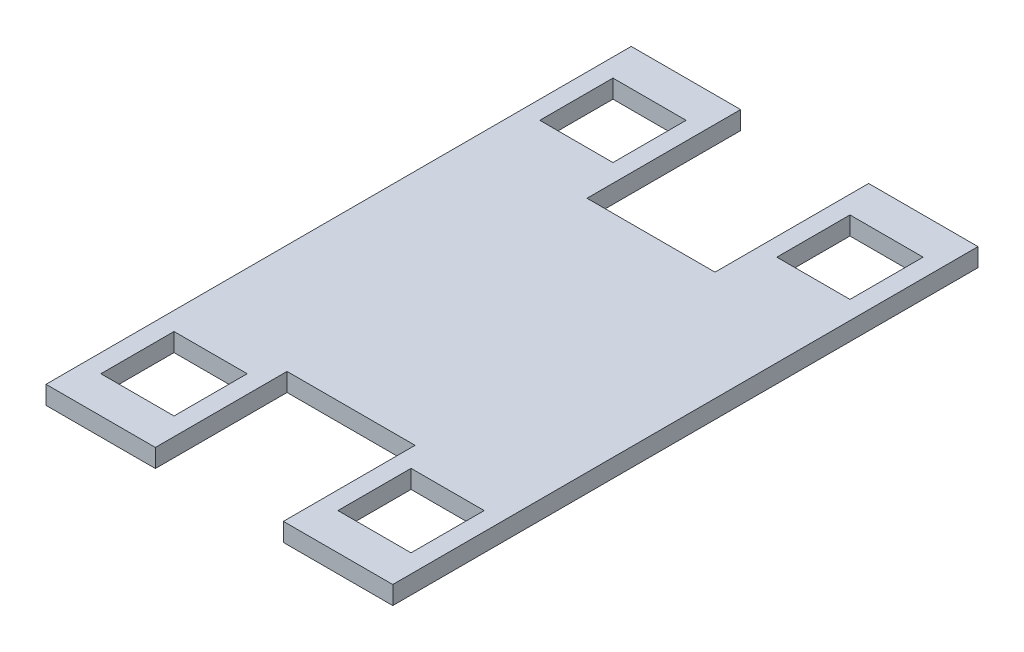
SolidWorks part; units mm, degrees
material "Balsa"
ref_plane "Front Plane" through (0, 0, 0) normal (0, 0, 1) x (1, 0, 0)
ref_plane "Top Plane" through (0, 0, 0) normal (0, 1, 0) x (1, 0, 0)
ref_plane "Right Plane" through (0, 0, 0) normal (1, 0, 0) x (0, 0, -1)
sketch "Sketch1" plane through (0, 0, 0) normal (0, 1, 0) x (1, 0, 0)
  line L1 (-60.198, 101.6) -> (60.198, 101.6)
  line L2 (-60.198, 101.6) -> (-60.198, -101.6)
  line L3 (-60.198, -101.6) -> (60.198, -101.6)
  line L4 (60.198, 101.6) -> (60.198, -101.6)
  line L5 (-60.198, 101.6) -> (60.198, -101.6) construction
  line L6 (-60.198, -101.6) -> (60.198, 101.6) construction
  point P0 (0, 0)
  dimension "D1" = 203.2
  dimension "D2" = 120.396
extrude "Boss-Extrude1" add sketch "Sketch1" along normal blind 6.35
sketch "Sketch2" plane through (0, 6.35, 0) normal (0, 1, 0) x (1, 0, 0)
  line L0 (-60.198, 101.6) -> (-60.198, -101.6) construction
  line L1 (-53.848, 88.9) -> (-28.448, 88.9)
  line L2 (-53.848, 88.9) -> (-53.848, 63.5)
  line L3 (-53.848, 63.5) -> (-28.448, 63.5)
  line L4 (-28.448, 88.9) -> (-28.448, 63.5)
  line L5 (-53.848, 88.9) -> (-28.448, 63.5) construction
  line L6 (-53.848, 63.5) -> (-28.448, 88.9) construction
  line L7 (60.198, 101.6) -> (-60.198, 101.6) construction
  point P0 (-41.148, 76.2)
  dimension "D1" = 6.35
  dimension "D2" = 12.7
  dimension "D3" = 25.4
extrude "Cut-Extrude1" cut sketch "Sketch2" against normal through all both and the other way through all
mirror "Mirror1" about plane through (0, 0, 0) normal (0, 0, 1) of "Cut-Extrude1"
mirror "Mirror2" about plane through (0, 0, 0) normal (1, 0, 0) of "Mirror1", "Cut-Extrude1"
sketch "Sketch3" plane through (0, 6.35, 0) normal (0, 1, 0) x (1, 0, 0)
  line L0 (0, -101.6) -> (0, 0) construction
  line L1 (-60.198, -101.6) -> (60.198, -101.6) construction
  line L2 (-22.225, -101.6) -> (22.225, -101.6)
  line L3 (-22.225, -101.6) -> (-22.225, -55.88)
  line L4 (22.225, -101.6) -> (22.225, -55.88)
  line L5 (-22.225, -55.88) -> (22.225, -55.88)
  line L6 (-22.225, -101.6) -> (22.225, -55.88) construction
  line L7 (22.225, -101.6) -> (-22.225, -55.88) construction
  line L8 (60.198, 101.6) -> (-60.198, 101.6) construction
  line L9 (53.848, -63.5) -> (28.448, -63.5) construction
  line L10 (-22.225, 48.26) -> (22.225, 48.26)
  line L11 (-22.225, 48.26) -> (-22.225, 101.6)
  line L12 (-22.225, 101.6) -> (22.225, 101.6)
  line L13 (22.225, 48.26) -> (22.225, 101.6)
  line L14 (-22.225, 48.26) -> (22.225, 101.6) construction
  line L15 (-22.225, 101.6) -> (22.225, 48.26) construction
  line L16 (53.848, 63.5) -> (28.448, 63.5) construction
  point P2 (0, 74.93)
  point P7 (0, -101.6)
  point P8 (0, -78.74)
  dimension "D1" = 44.45
  dimension "D2" = 7.62
  dimension "D3" = 44.45
  dimension "D4" = 15.24
extrude "Cut-Extrude2" cut sketch "Sketch3" against normal through all
